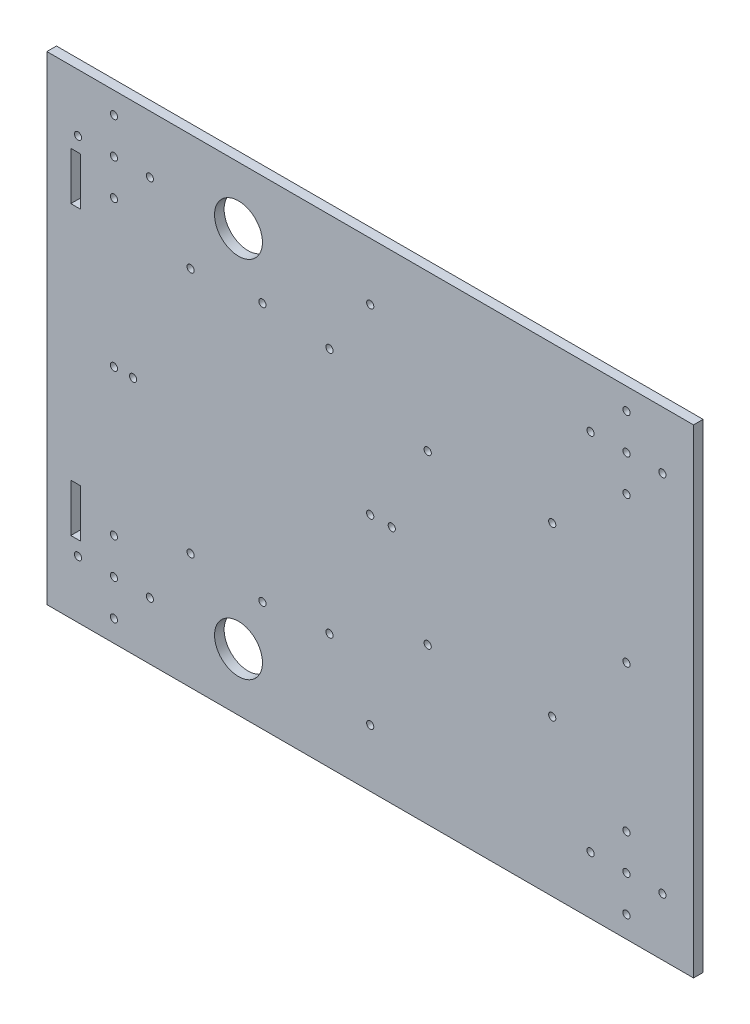
SolidWorks part; units mm, degrees
material "Acrylic (Medium-high impact)"
ref_plane "Front Plane" through (0, 0, 0) normal (0, 0, 1) x (1, 0, 0)
ref_plane "Top Plane" through (0, 0, 0) normal (0, 1, 0) x (1, 0, 0)
ref_plane "Right Plane" through (0, 0, 0) normal (1, 0, 0) x (0, 0, -1)
sketch "Sketch1" plane through (0, 0, 0) normal (0, 0, 1) x (1, 0, 0)
  line L1 (-63.2367, 83.8667) -> (206.7633, 83.8667)
  line L2 (-63.2367, 83.8667) -> (-63.2367, -116.1333)
  line L3 (-63.2367, -116.1333) -> (206.7633, -116.1333)
  line L4 (206.7633, 83.8667) -> (206.7633, -116.1333)
  line L5 (-20.2367, -92.1333) -> (193.7633, -92.1333) construction
  line L6 (-20.2367, -92.1333) -> (-20.2367, 59.8667) construction
  line L7 (71.7633, -16.1333) -> (178.7633, -16.1333) construction
  line L8 (71.7633, -16.1333) -> (-35.2367, -16.1333) construction
  line L9 (-53.2367, 53.8667) -> (-49.2367, 53.8667)
  line L10 (-53.2367, 53.8667) -> (-53.2367, 33.8667)
  line L11 (-53.2367, 33.8667) -> (-49.2367, 33.8667)
  line L12 (-49.2367, 53.8667) -> (-49.2367, 33.8667)
  line L13 (-53.2367, -66.1333) -> (-49.2367, -66.1333)
  line L14 (-53.2367, -66.1333) -> (-53.2367, -86.1333)
  line L15 (-53.2367, -86.1333) -> (-49.2367, -86.1333)
  line L16 (-49.2367, -66.1333) -> (-49.2367, -86.1333)
  circle A0 centre (-35.2367, -92.1333) radius 1.5
  circle A1 centre (-20.2367, -92.1333) radius 1.5
  circle A2 centre (-35.2367, -107.1333) radius 1.5
  circle A3 centre (-50.2367, -92.1333) radius 1.5
  circle A4 centre (-35.2367, -77.1333) radius 1.5
  circle A5 centre (71.7633, -16.1333) radius 1.5
  circle A6 centre (193.7633, -92.1333) radius 1.5
  circle A7 centre (178.7633, -77.1333) radius 1.5
  circle A8 centre (178.7633, -92.1333) radius 1.5
  circle A9 centre (178.7633, -107.1333) radius 1.5
  circle A10 centre (163.7633, -92.1333) radius 1.5
  circle A11 centre (193.7633, 59.8667) radius 1.5
  circle A12 centre (178.7633, 74.8667) radius 1.5
  circle A13 centre (178.7633, 59.8667) radius 1.5
  circle A14 centre (178.7633, 44.8667) radius 1.5
  circle A15 centre (163.7633, 59.8667) radius 1.5
  circle A16 centre (-20.2367, 59.8667) radius 1.5
  circle A17 centre (-35.2367, 74.8667) radius 1.5
  circle A18 centre (-35.2367, 59.8667) radius 1.5
  circle A19 centre (-35.2367, 44.8667) radius 1.5
  circle A20 centre (-50.2367, 59.8667) radius 1.5
  circle A21 centre (178.7633, -16.1333) radius 1.5
  circle A22 centre (95.7633, 18.8667) radius 1.5
  circle A23 centre (71.7633, 59.8667) radius 1.5
  circle A24 centre (16.7633, 59.8667) radius 10
  circle A25 centre (16.7633, -92.1333) radius 10
  circle A26 centre (-35.2367, -16.1333) radius 1.5
  circle A27 centre (-35.2367, -92.1333) radius 1.5 [skipped]
  circle A28 centre (71.7633, -92.1333) radius 1.5
  circle A29 centre (26.7633, -16.1333) radius 46
  circle A30 centre (26.7633, -70.1333) radius 1.5
  circle A31 centre (-27.2367, -16.1333) radius 1.5
  circle A32 centre (26.7633, 37.8667) radius 1.5
  circle A33 centre (80.7633, -16.1333) radius 1.5
  circle A34 centre (178.7633, 59.8667) radius 1.5 [skipped]
  circle A35 centre (147.7633, 18.8667) radius 1.5
  circle A36 centre (147.7633, -51.1333) radius 1.5
  circle A37 centre (95.7633, -51.1333) radius 1.5
  circle A38 centre (-3.2367, 35.3667) radius 1.5
  circle A39 centre (54.7633, 35.3667) radius 1.5
  circle A40 centre (54.7633, -67.6333) radius 1.5
  circle A41 centre (-3.2367, -67.6333) radius 1.5
  point P28 (-35.2367, -92.1333)
  point P83 (-6.0985, -16.1333)
  point P84 (26.7633, -16.1333)
  point P99 (26.7633, -16.1333)
  dimension "D3" = 24
  dimension "D4" = 2
  dimension "D5" = 15
  dimension "D9" = 2
  dimension "D7" = 80
  dimension "D8" = 2
  dimension "D16" = 2
  dimension "D21" = 24
  dimension "D23" = 90
  dimension "D27" = 10
  dimension "D28" = 30
  dimension "D24" = 15
  dimension "D26" = 54
  dimension "D31" = 28
  dimension "D32" = 100
  dimension "D33" = 2
  dimension "D35" = 65
  dimension "D36" = 2
  dimension "D37" = 2
  dimension "D38" = 48.5
  dimension "D10" = 9
  dimension "D11" = 28
  dimension "D12" = 200
  dimension "D13" = 270
  dimension "D14" = 214
  dimension "D15" = 152
  dimension "D17" = 107
  dimension "D20" = 107
  dimension "D22" = 2
  dimension "D29" = 10
  dimension "D30" = 30
  dimension "D39" = 60
  dimension "D18" = 2
  dimension "D19" = 2
  dimension "D34" = 2
  dimension "D6" = 4
  dimension "D25" = 4
extrude "Boss-Extrude1" add sketch "Sketch1" along normal blind 4 contours L4 L1 L2 L3 A28 A26 A0 A1 A2 A3 A4 A5 A6 A7 A8 A9 A10 A11 A12 A13 A14 A15 A16 A17 A18 A19 A20 | A29 A26
